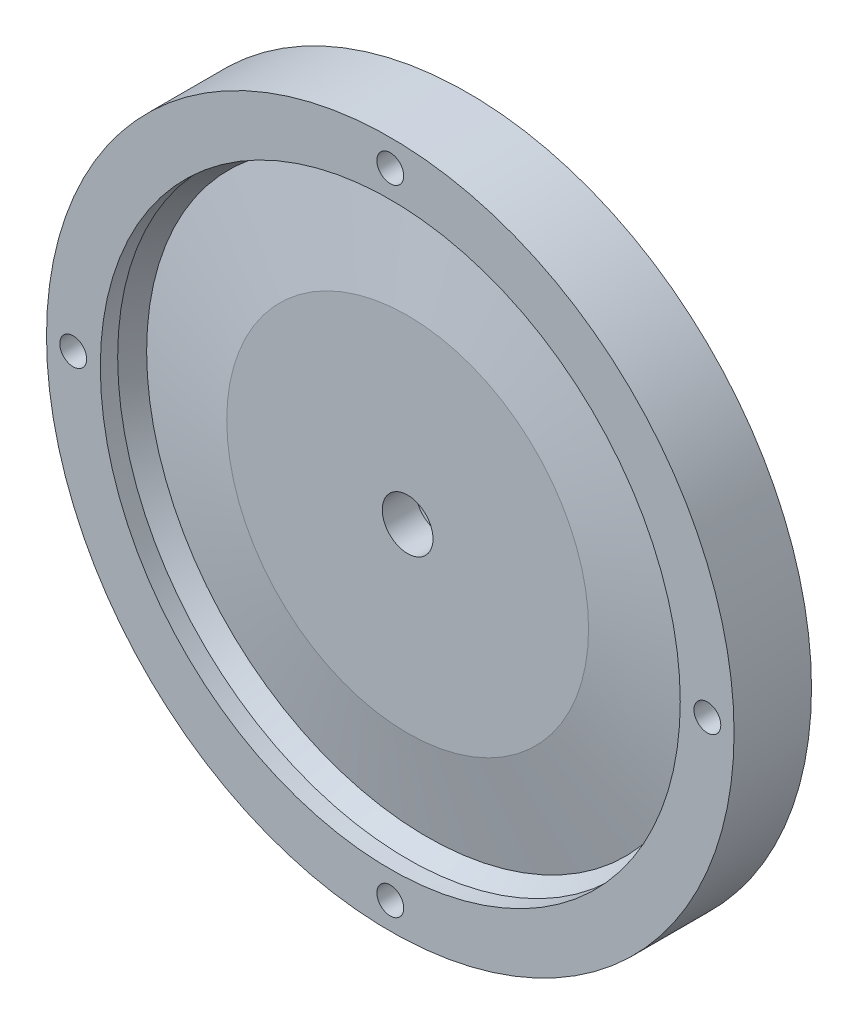
SolidWorks part; units mm, degrees
ref_plane "Front Plane" through (0, 0, 0) normal (0, 0, 1) x (1, 0, 0)
ref_plane "Top Plane" through (0, 0, 0) normal (0, 1, 0) x (1, 0, 0)
ref_plane "Right Plane" through (0, 0, 0) normal (1, 0, 0) x (0, 0, -1)
sketch "Sketch1" plane through (0, 0, 0) normal (0, 0, 1) x (1, 0, 0)
  circle A0 centre (0, 0) radius 65.405
  dimension "D1" = 130.81
extrude "Boss-Extrude1" add sketch "Sketch1" along normal blind 14.732
sketch "Sketch2" plane through (0, 0, 14.732) normal (0, 0, 1) x (1, 0, 0)
  circle A0 centre (0, 0) radius 55.1688
  circle A1 centre (0, 0) radius 65.405 construction
  dimension "D1" = 10.2362
extrude "Cut-Extrude1" cut sketch "Sketch2" against normal blind 3.302
sketch "Sketch3" plane through (0, 0, 0) normal (1, 0, 0) x (0, 0, -1)
  line L0 (-11.43, 34.417) -> (-7.747, 53.34)
  line L1 (-11.43, 55.1688) -> (-11.43, -55.1688) construction
  line L2 (-7.747, 53.34) -> (-11.43, 55.1688)
  line L3 (-11.43, 55.1688) -> (-11.43, 34.417)
  line L4 (0, 0) -> (-14.732, 0) construction
  line L5 (0, -65.405) -> (0, 65.405) construction
  line L6 (-14.732, 65.405) -> (-14.732, -65.405) construction
  dimension "D1" = 34.417
  dimension "D2" = 6.985
  dimension "D3" = 53.34
revolve "Cut-Revolve1" cut sketch "Sketch3" angle 360 about L4
hole_wizard "1/4-20 Tapped Hole1" positions "Sketch5" profile "Sketch4" tap size "1/4-20" standard "ANSI Inch" end condition through all
sketch "Sketch5" plane through (0, 0, 14.732) normal (0, 0, 1) x (1, 0, 0)
  point P0 (0, 60.325)
  point P2 (60.325, 0)
  point P4 (0, -60.325)
  point P6 (-60.325, 0)
  dimension "D1" = 60.325
  dimension "D2" = 60.325
  dimension "D3" = 60.325
  dimension "D4" = 60.325
sketch "Sketch4" plane through (0, 60.325, 14.732) normal (1, 0, 0) x (0, -1, 0)
  line L0 (0, 0) -> (0, 14.732)
  line L1 (0, 14.732) -> (2.5527, 14.732)
  line L2 (2.5527, 14.732) -> (2.5527, 0)
  line L5 (2.5527, 0) -> (0, 0)
  line L11 (0, -6.35) -> (0, 107.95) construction
  dimension "Thru Tap Drill Dia." = 5.1054
  dimension "Thru Tap Drill Depth" = 14.732
cosmetic thread "Hole Thread1" parameters "D2"=6.35
cosmetic thread "Hole Thread2" parameters "D2"=6.35
cosmetic thread "Hole Thread3" parameters "D2"=6.35
cosmetic thread "Hole Thread4" parameters "D2"=6.35
sketch "Sketch6" plane through (0, 0, 0) normal (0, 0, -1) x (-1, 0, 0)
  circle A0 centre (0, 0) radius 45.72
  dimension "D1" = 91.44
extrude "Cut-Extrude2" cut sketch "Sketch6" against normal blind 5.08
sketch "Sketch7" plane through (0, 0, 5.08) normal (0, 0, -1) x (-1, 0, 0)
  circle A0 centre (0, 0) radius 4.826
  dimension "D1" = 9.652
extrude "Cut-Extrude3" cut sketch "Sketch7" against normal through all
sketch "Sketch8" plane through (0, 0, 5.08) normal (0, 0, -1) x (-1, 0, 0)
  line L0 (-45.72, 0) -> (45.72, 0) construction
  line L1 (-13.2932, -6.35) -> (-9.4273, -6.35)
  line L2 (-13.2932, 6.35) -> (-9.4273, 6.35)
  line L3 (-45.72, 6.35) -> (45.72, 6.35) construction
  line L4 (9.4273, 6.35) -> (13.2932, 6.35)
  line L5 (-45.72, -6.35) -> (45.72, -6.35) construction
  line L6 (9.4273, -6.35) -> (13.2932, -6.35)
  arc A0 (-13.2932, -6.35) -> (13.2932, -6.35) centre (0, 0) ccw
  arc A1 (-9.4273, -6.35) -> (9.4273, -6.35) centre (0, 0) ccw
  circle A2 centre (0, 0) radius 45.72 construction
  circle A3 centre (0, 0) radius 45.72 construction
  arc A4 (9.4273, 6.35) -> (-9.4273, 6.35) centre (0, 0) ccw
  arc A5 (13.2932, 6.35) -> (-13.2932, 6.35) centre (0, 0) ccw
  dimension "D1" = 29.464
  dimension "D4" = 22.733
  dimension "D2" = 6.35
  dimension "D3" = 6.35
extrude "Boss-Extrude2" add sketch "Sketch8" along normal blind 6.223
